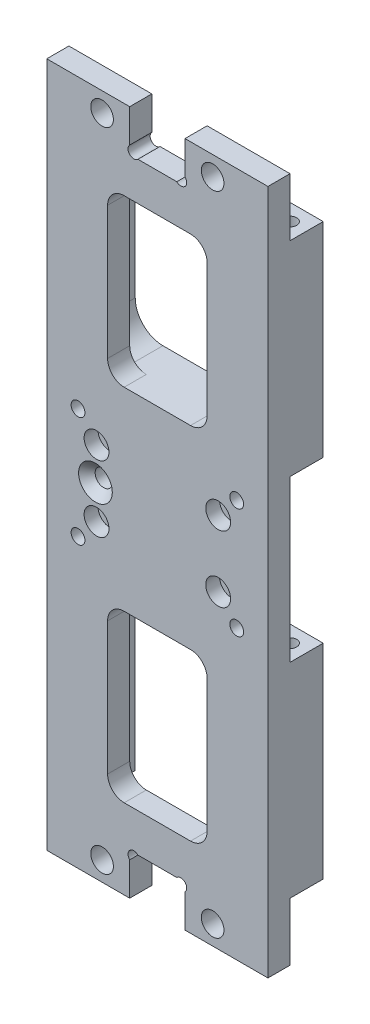
SolidWorks part; units mm, degrees
material "6061 合金"
ref_plane "前视基准面" through (0, 0, 0) normal (0, 0, 1) x (1, 0, 0)
ref_plane "上视基准面" through (0, 0, 0) normal (0, 1, 0) x (1, 0, 0)
ref_plane "右视基准面" through (0, 0, 0) normal (1, 0, 0) x (0, 0, -1)
sketch "草图1" plane through (0, 0, 0) normal (0, 0, 1) x (1, 0, 0)
  line L0 (0, -62) -> (0, 62) construction
  line L5 (20, -62) -> (5, -62)
  line L6 (20, -62) -> (20, 62)
  line L7 (20, 62) -> (5, 62)
  line L8 (-20, -62) -> (-20, 62)
  line L9 (0, 0) -> (100.9515, 0) construction
  line L10 (0, 58.5) -> (10, 58.5) construction
  line L11 (5, -62) -> (5, -54.5)
  line L12 (11, 6) -> (-11, 6) construction
  line L13 (11, 6) -> (11, -6) construction
  line L14 (11, -6) -> (-11, -6) construction
  line L15 (-11, 6) -> (-11, -6) construction
  line L16 (11, 6) -> (-11, -6) construction
  line L17 (11, -6) -> (-11, 6) construction
  line L18 (14.35, 10) -> (-14.35, 10) construction
  line L19 (14.35, 10) -> (14.35, -10) construction
  line L20 (14.35, -10) -> (-14.35, -10) construction
  line L21 (-14.35, 10) -> (-14.35, -10) construction
  line L22 (-11.2, 0) -> (-11, 0) construction
  line L23 (-14.35, -10) -> (14.35, 10) construction
  line L24 (5, -54.5) -> (-5, -54.5)
  line L25 (-5, -54.5) -> (-5, -62)
  line L26 (5, -62) -> (0, -62) construction
  line L27 (-5, -62) -> (-20, -62)
  line L28 (0, -62) -> (-5, -62) construction
  line L29 (-5, 54.5) -> (-5, 62)
  line L30 (5, 54.5) -> (-5, 54.5)
  line L31 (5, 62) -> (5, 54.5)
  line L32 (5, 62) -> (0, 62) construction
  line L33 (-5, 62) -> (-20, 62)
  line L34 (0, 62) -> (-5, 62) construction
  circle A4 centre (10, 58.5) radius 2.05
  circle A5 centre (-10, 58.5) radius 2.05
  circle A6 centre (10, -58.5) radius 2.05
  circle A7 centre (-10, -58.5) radius 2.05
  circle A8 centre (-11, 6) radius 1.05
  circle A9 centre (-11, -6) radius 1.05
  circle A10 centre (11, -6) radius 1.05
  circle A11 centre (11, 6) radius 1.05
  circle A12 centre (-11.2, 0) radius 1.55
  circle A13 centre (-14.35, -10) radius 1.25
  circle A14 centre (-14.35, 10) radius 1.25
  circle A15 centre (14.35, 10) radius 1.25
  circle A16 centre (14.35, -10) radius 1.25
  point P4 (0, 0)
  point P9 (0, 0)
  point P35 (0, 0)
  point P44 (0, -54.5)
  dimension "D2" = 117
  dimension "D3" = 7.5
  dimension "D5" = 4.1
  dimension "D9" = 2.1
  dimension "D10" = 3.1
  dimension "D13" = 2.5
  dimension "D17" = 0.2
  dimension "D1" = 124
  dimension "D4" = 10
  dimension "D6" = 10
  dimension "D7" = 22
  dimension "D8" = 12
  dimension "D11" = 20
  dimension "D12" = 28.7
  dimension "D15" = 10
extrude "凸台-拉伸1" add sketch "草图1" along normal blind 4
cosmetic thread "装饰螺纹线1" parameters "D2"=3
cosmetic thread "装饰螺纹线2" parameters "D2"=3
cosmetic thread "装饰螺纹线3" parameters "D2"=3
cosmetic thread "装饰螺纹线4" parameters "D2"=3
sketch "草图3" plane through (0, 0, 4) normal (0, 0, 1) x (1, 0, 0)
  line L0 (-20, 14.55) -> (20, 14.55)
  line L3 (0, 0) -> (34.5176, 0) construction
  line L8 (14, -17.55) -> (-14, -17.55)
  line L9 (20, -14.55) -> (20, -51.5)
  line L10 (-20, -14.55) -> (20, -14.55)
  line L11 (-20, 62) -> (-20, -62) construction
  line L12 (20, -51.5) -> (14, -51.5)
  line L13 (14, -51.5) -> (14, -17.55)
  line L15 (0, -55) -> (0, 55) construction
  line L16 (-20, -14.55) -> (-20, -51.5)
  line L17 (-20, -51.5) -> (-14, -51.5)
  line L18 (-14, -51.5) -> (-14, -17.55)
  line L19 (-20, 14.55) -> (-20, 51.5)
  line L20 (-20, 51.5) -> (-14, 51.5)
  line L21 (-14, 51.5) -> (-14, 17.55)
  line L22 (14, 17.55) -> (-14, 17.55)
  line L23 (14, 51.5) -> (14, 17.55)
  line L24 (20, 51.5) -> (14, 51.5)
  line L25 (20, 14.55) -> (20, 51.5)
  circle A0 centre (10, -58.5) radius 2.05 construction
  dimension "D1" = 29.1
  dimension "D2" = 3
  dimension "D3" = 6
  dimension "D4" = 7
extrude "凸台-拉伸2" add sketch "草图3" against normal blind 6 from surface at -4 starting at face at (0, 0, 0)
sketch "草图4" plane through (0, 0, 4) normal (0, 0, 1) x (1, 0, 0)
  line L0 (5, -55.9849) -> (3.5151, -54.5) construction
  line L1 (-5, -54.5) -> (5, -54.5) construction
  line L2 (5, -54.5) -> (5, -62) construction
  line L3 (-5, -55.9849) -> (-3.5151, -54.5) construction
  line L4 (-5, -62) -> (-5, -54.5) construction
  line L5 (-5, -54.5) -> (5, -54.5) construction
  line L6 (55, 0) -> (-55, 0) construction
  line L7 (-5, 55.9849) -> (-3.5151, 54.5) construction
  line L8 (5, 55.9849) -> (3.5151, 54.5) construction
  circle A2 centre (-4.2575, -55.2425) radius 1.05
  circle A3 centre (4.2575, -55.2425) radius 1.05
  circle A4 centre (4.2575, 55.2425) radius 1.05
  circle A5 centre (-4.2575, 55.2425) radius 1.05
  dimension "D1" = 2.1
  dimension "D2" = 45
  dimension "D3" = 45
extrude "切除-拉伸2" cut sketch "草图4" against normal through all
sketch "草图5" plane through (0, -51.5, 0) normal (0, -1, 0) x (1, 0, 0)
  line L0 (20, -3) -> (-20, -3) construction
  line L3 (0, 0) -> (0, -11.1984) construction
  line L4 (20, -6) -> (20, 0) construction
  line L5 (-20, -6) -> (-20, 0) construction
  circle A0 centre (17, -3) radius 1.2
  circle A1 centre (-17, -3) radius 1.2
  dimension "D1" = 2.4
  dimension "D2" = 3
extrude "切除-拉伸3" cut sketch "草图5" against normal through all
cosmetic thread "装饰螺纹线5" parameters "D2"=3
cosmetic thread "装饰螺纹线6" parameters "D2"=3
cosmetic thread "装饰螺纹线7" parameters "D2"=3
cosmetic thread "装饰螺纹线8" parameters "D2"=3
fillet "圆角1" radius 5 4 edges at (-14, 17.55, -3) (14, 17.55, -3) (-14, -17.55, -3) (14, -17.55, -3)
sketch "草图6" plane through (0, 0, 4) normal (0, 0, 1) x (1, 0, 0)
  circle A0 centre (-11, -6) radius 2.25
  circle A1 centre (-11, 6) radius 2.25
  circle A2 centre (11, 6) radius 2.25
  circle A3 centre (11, -6) radius 2.25
  dimension "D1" = 4.5
extrude "切除-拉伸4" cut sketch "草图6" against normal blind 2.5
chamfer "倒角1" distance 1.5 angle 45 1 edges at (-9.65, 0, 4)
sketch "草图8" plane through (0, 0, 4) normal (0, 0, 1) x (1, 0, 0)
  line L0 (-9, -17.55) -> (9, -17.55) construction
  line L1 (6, -17.55) -> (-6, -17.55)
  line L2 (9, -20.55) -> (9, -44.55)
  line L3 (6, -47.55) -> (-6, -47.55)
  line L4 (-9, -20.55) -> (-9, -44.55)
  line L5 (0, 0) -> (28.5787, 0) construction
  line L6 (-9, 20.55) -> (-9, 44.55)
  line L7 (6, 47.55) -> (-6, 47.55)
  line L8 (9, 20.55) -> (9, 44.55)
  line L9 (6, 17.55) -> (-6, 17.55)
  arc A0 (-9, -17.55) -> (-14, -22.55) centre (-9, -22.55) ccw construction
  arc A1 (-6, -17.55) -> (-9, -20.55) centre (-6, -20.55) ccw
  arc A2 (9, -44.55) -> (6, -47.55) centre (6, -44.55) cw
  arc A3 (-6, -47.55) -> (-9, -44.55) centre (-6, -44.55) cw
  arc A4 (6, -17.55) -> (9, -20.55) centre (6, -20.55) cw
  arc A5 (6, 17.55) -> (9, 20.55) centre (6, 20.55) ccw
  arc A6 (-6, 47.55) -> (-9, 44.55) centre (-6, 44.55) ccw
  arc A7 (9, 44.55) -> (6, 47.55) centre (6, 44.55) ccw
  arc A8 (-6, 17.55) -> (-9, 20.55) centre (-6, 20.55) cw
  point P15 (-9, -17.55)
  point P18 (9, -47.55)
  point P23 (9, -17.55)
  point P36 (9, 17.55)
  point P37 (9, 47.55)
  point P38 (-9, 17.55)
  dimension "D2" = 3
  dimension "D1" = 30
extrude "切除-拉伸6" cut sketch "草图8" against normal through all both and the other way through all
